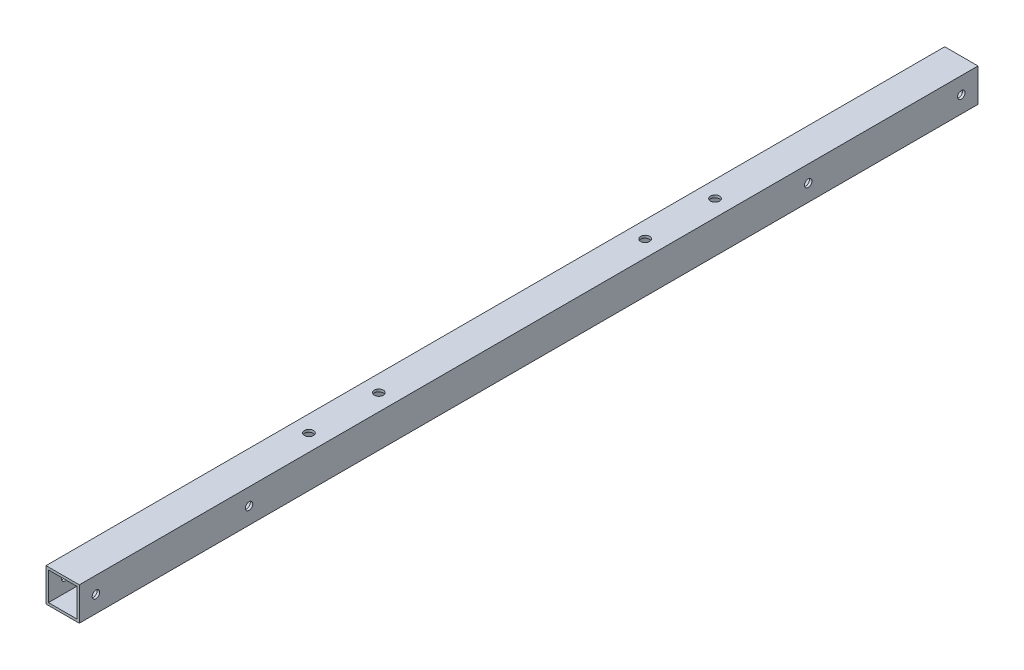
SolidWorks part; units mm, degrees
material "6063-T5"
ref_plane "正面" through (0, 0, 0) normal (0, 0, 1) x (1, 0, 0)
ref_plane "平面" through (0, 0, 0) normal (0, 1, 0) x (1, 0, 0)
ref_plane "右側面" through (0, 0, 0) normal (1, 0, 0) x (0, 0, -1)
sketch "ｽｹｯﾁ1" plane through (0, 0, 0) normal (0, 0, 1) x (1, 0, 0)
  line L1 (-10, -10) -> (10, -10)
  line L2 (-10, -10) -> (-10, 10)
  line L3 (-10, 10) -> (10, 10)
  line L4 (10, -10) -> (10, 10)
  line L5 (-10, -10) -> (10, 10) construction
  line L6 (-10, 10) -> (10, -10) construction
  line L7 (-8.5, -8.5) -> (8.5, -8.5)
  line L8 (-8.5, -8.5) -> (-8.5, 8.5)
  line L9 (-8.5, 8.5) -> (8.5, 8.5)
  line L10 (8.5, -8.5) -> (8.5, 8.5)
  line L11 (-8.5, -8.5) -> (8.5, 8.5) construction
  line L12 (-8.5, 8.5) -> (8.5, -8.5) construction
  point P0 (0, 0)
  point P6 (0, 0)
  dimension "D1" = 1.5
  dimension "D2" = 20
  dimension "D3" = 20
extrude "ﾎﾞｽ - 押し出し1" add sketch "ｽｹｯﾁ1" along normal blind 540
sketch "ｽｹｯﾁ3" plane through (10, 0, 0) normal (1, 0, 0) x (0, 0, -1)
  line L0 (-540, -10) -> (-540, 10) construction
  line L1 (-540, -10) -> (0, -10) construction
  circle A0 centre (-530, 0) radius 2.25
  circle A16 centre (-438, 0) radius 2.25
  circle A17 centre (-102, 0) radius 2.25
  circle A18 centre (-10, 0) radius 2.25
  dimension "D1" = 10
  dimension "D2" = 4.5
  dimension "D3" = 10
  dimension "D7" = 10
  dimension "D5" = 92
  dimension "D4" = 2
  dimension "D6" = 2
extrude "ｶｯﾄ - 押し出し2" cut sketch "ｽｹｯﾁ3" against normal blind 20
sketch "ｽｹｯﾁ4" plane through (0, 10, 0) normal (0, 1, 0) x (1, 0, 0)
  line L0 (-10, -270) -> (10, -270) construction
  line L1 (-10, -540) -> (-10, 0) construction
  line L2 (10, -540) -> (10, 0) construction
  point P0 (0, -148)
  point P1 (0, -190)
  point P8 (0, -270)
  point P10 (0, -350)
  point P11 (0, -392)
  dimension "D1" = 80
  dimension "D2" = 42
hole_wizard "Ø5.4 (5.4) 直径の穴1" positions "ｽｹｯﾁ4" profile "ｽｹｯﾁ5" hole size "Ø5.4" standard "JIS" end condition through all
sketch "ｽｹｯﾁ5" plane through (0, 10, 148) normal (1, 0, 0) x (0, 0, 1)
  line L0 (0, 0) -> (0, 20)
  line L1 (0, 20) -> (2.7, 20)
  line L2 (2.7, 20) -> (2.7, 0)
  line L5 (2.7, 0) -> (0, 0)
  line L11 (0, -6.35) -> (0, 107.95) construction
  dimension "通し穴の直径" = 5.4
  dimension "通し穴の深さ" = 20
hole_wizard "Ø10.0 (10) 直径の穴1" positions "ｽｹｯﾁ6" profile "ｽｹｯﾁ8" hole size "Ø10.0" standard "JIS"
sketch "ｽｹｯﾁ6" plane through (0, -10, 0) normal (0, -1, 0) x (-1, 0, 0)
  point P0 (0, -148)
  point P3 (0, -190)
  point P6 (0, -350)
  point P9 (0, -392)
sketch "ｽｹｯﾁ8" plane through (0, -10, 148) normal (1, 0, 0) x (0, 0, -1)
  line L0 (0, 0) -> (0, 1.5)
  line L1 (0, 1.5) -> (5, 1.5)
  line L2 (5, 1.5) -> (5, 0)
  line L5 (5, 0) -> (0, 0)
  line L10 (0, 1.5) -> (-5, 1.5) construction
  line L11 (0, -6.35) -> (0, 107.95) construction
  dimension "穴の直径" = 10
  dimension "穴の深さ" = 1.5
  dimension "ﾄﾞﾘﾙ角度" = 180
